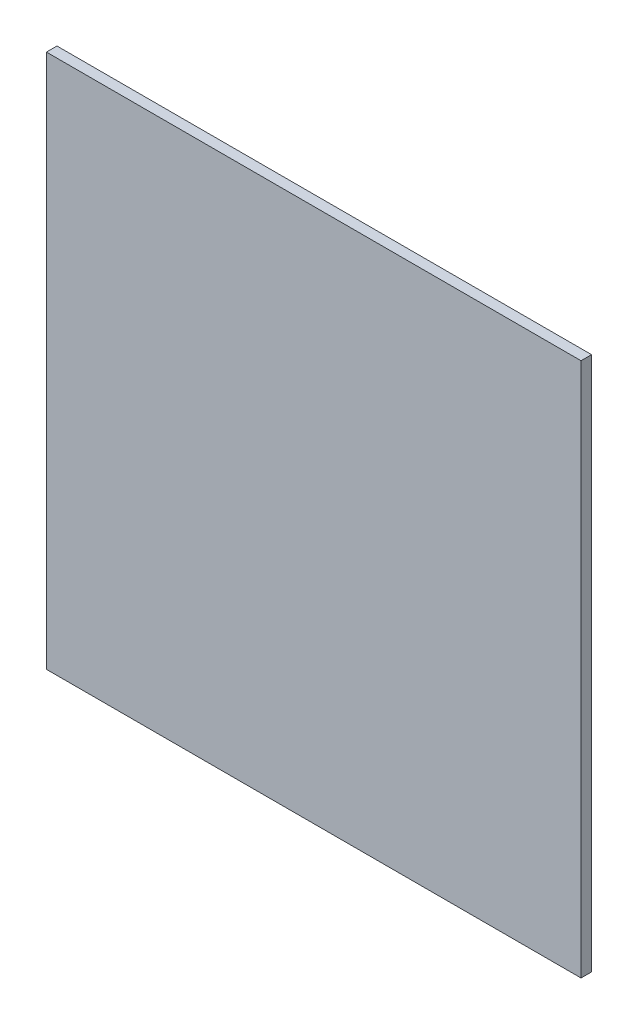
SolidWorks part; units mm, degrees
ref_plane "Front Plane" through (0, 0, 0) normal (0, 0, 1) x (1, 0, 0)
ref_plane "Top Plane" through (0, 0, 0) normal (0, 1, 0) x (1, 0, 0)
ref_plane "Right Plane" through (0, 0, 0) normal (1, 0, 0) x (0, 0, -1)
sketch "Sketch1" plane through (0, 0, 0) normal (0, 0, 1) x (1, 0, 0)
  line L0 (-17.5687, 0) -> (14.6406, 0) construction
  line L1 (-101.6, 101.6) -> (101.6, 101.6)
  line L2 (-101.6, 101.6) -> (-101.6, -101.6)
  line L3 (-101.6, -101.6) -> (101.6, -101.6)
  line L4 (101.6, 101.6) -> (101.6, -101.6)
  line L5 (0, 17.2759) -> (0, -17.2759) construction
  dimension "D1" = 203.2
extrude "Boss-Extrude1" add sketch "Sketch1" along normal blind 4
